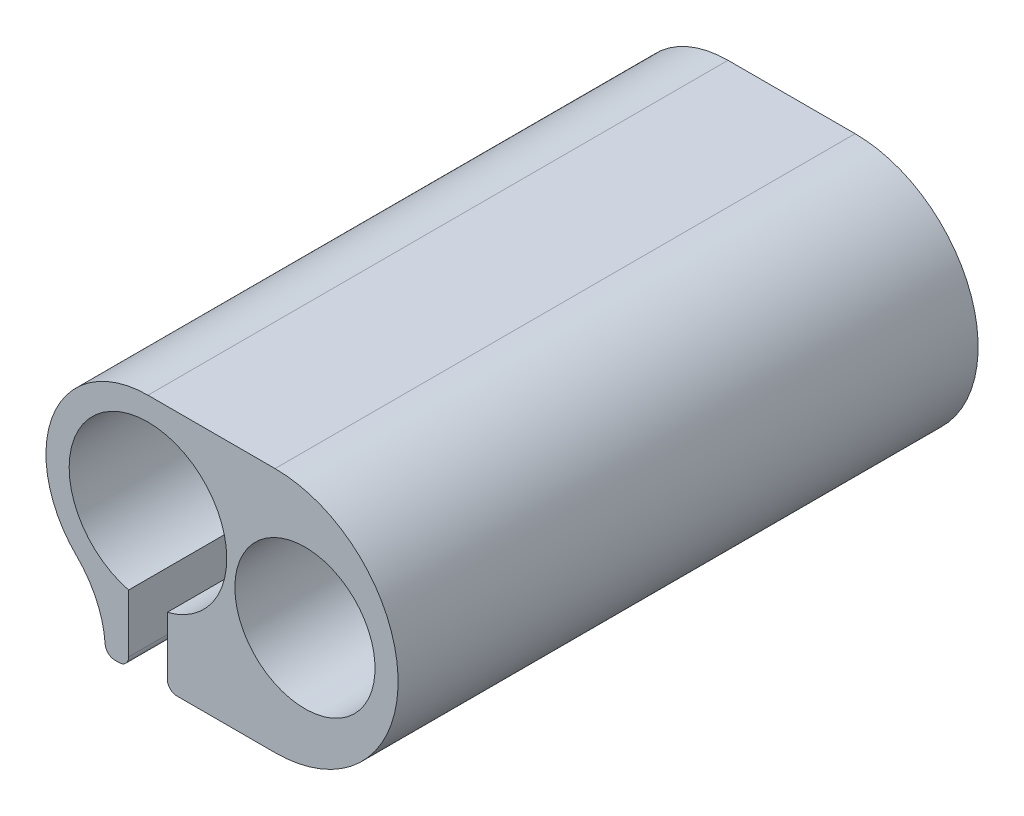
SolidWorks part; units mm, degrees
ref_plane "Plan de face" through (0, 0, 0) normal (0, 0, 1) x (1, 0, 0)
ref_plane "Plan de dessus" through (0, 0, 0) normal (0, 1, 0) x (1, 0, 0)
ref_plane "Plan de droite" through (0, 0, 0) normal (1, 0, 0) x (0, 0, -1)
sketch "Esquisse1" plane through (0, 0, 0) normal (0, 0, 1) x (1, 0, 0)
  line L0 (-2, -7.9008) -> (-2, -14.9008)
  line L1 (2, -7.9008) -> (2, -14.9008)
  line L2 (-4.4, -9.5887) -> (-4.4, -14.9008)
  line L4 (-4.4, -14.9008) -> (-2, -14.9008)
  line L6 (2, -14.9008) -> (4.4, -14.9008)
  line L8 (0, 10.55) -> (0, -14.9008) construction
  line L9 (0, -2.1754) -> (28.95, -2.1754) construction
  line L10 (13.1471, 10.55) -> (0, 10.55)
  line L11 (4.4, -14.9008) -> (13.1471, -14.9008)
  line L13 (4.4, -9.5887) -> (4.4, -14.9008) construction
  arc A0 (-2, -7.9008) -> (2, -7.9008) centre (0, 0) cw
  arc A1 (-4.4, -9.5887) -> (0, 10.55) centre (0, 0) cw
  arc A2 (13.1471, 10.55) -> (13.1471, -14.9008) centre (13.1471, -2.1754) cw
  arc A4 (-4.4, -9.5887) -> (4.4, -9.5887) centre (0, 0) cw construction
  dimension "D1" = 7
  dimension "D2" = 8.15
  dimension "D4" = 2.4
  dimension "D3" = 4
extrude "Boss.-Extru.1" add sketch "Esquisse1" along normal blind 60
sketch "Esquisse2" plane through (0, 0, 0) normal (0, 0, -1) x (-1, 0, 0)
  line L0 (-25.8725, -2.1754) -> (-12.684, -2.1754) construction
  arc A0 (-13.1471, 10.55) -> (-13.1471, -14.9008) centre (-13.1471, -2.1754) ccw construction
  circle A1 centre (-16.239, -2.1754) radius 7.25
  dimension "D1" = 14.5
extrude "Enlèv. mat.-Extru.1" cut sketch "Esquisse2" against normal through all
fillet "Congé1" radius 10 1 edges at (-4.4, -9.5887, 30)
fillet "Congé2" radius 1 3 edges at (-4.4, -14.9008, 30) (-2, -14.9008, 30) (2, -14.9008, 30)
